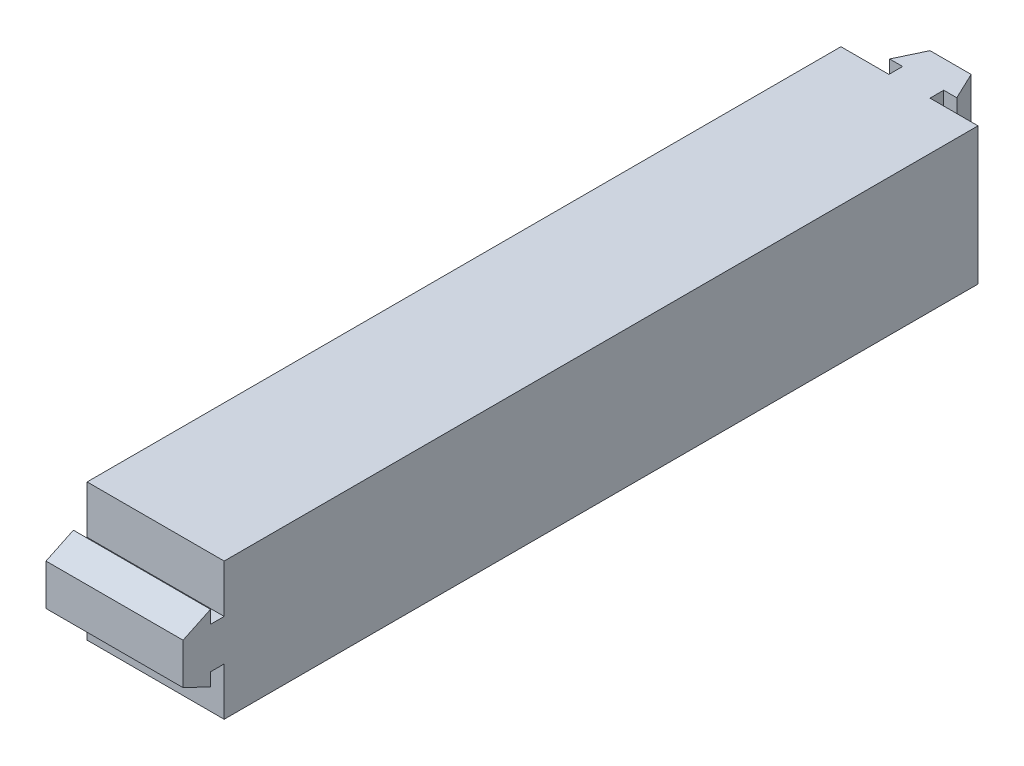
SolidWorks part; units mm, degrees
ref_plane "Front Plane" through (0, 0, 0) normal (0, 0, 1) x (1, 0, 0)
ref_plane "Top Plane" through (0, 0, 0) normal (0, 1, 0) x (1, 0, 0)
ref_plane "Right Plane" through (0, 0, 0) normal (1, 0, 0) x (0, 0, -1)
sketch "Sketch1" plane through (0, 0, 0) normal (0, 1, 0) x (1, 0, 0)
  line L1 (0, 0) -> (20, 0)
  line L2 (0, 0) -> (0, 110)
  line L4 (20, 0) -> (20, 110)
  line L5 (0, 110) -> (20, 110)
  point P1 (1.1497, 110)
  dimension "D1" = 110
  dimension "D4" = 20
extrude "Boss-Extrude1" add sketch "Sketch1" along normal blind 20
sketch "Sketch3" plane through (0, 0, 0) normal (1, 0, 0) x (0, 0, -1)
  line L0 (0, 10) -> (-6, 10) construction
  line L1 (0, 20) -> (0, 0) construction
  line L2 (0, 7) -> (0, 13)
  line L3 (0, 13) -> (-2, 13)
  line L4 (-2, 13) -> (-2, 14.9)
  line L5 (-2, 14.9) -> (-6, 13)
  line L6 (-6, 13) -> (-6, 7)
  line L7 (-2, 5.1) -> (-6, 7)
  line L8 (-2, 7) -> (-2, 5.1)
  line L9 (0, 7) -> (-2, 7)
  dimension "D1" = 6
  dimension "D2" = 3
  dimension "D3" = 2
  dimension "D4" = 1.9
  dimension "D5" = 3
extrude "Boss-Extrude3" add sketch "Sketch3" along normal up to surface (20 mm away) up to face at (20, 10, -55)
sketch "Sketch5" plane through (0, 20, 0) normal (0, 1, 0) x (1, 0, 0)
  line L0 (10, 110) -> (10, 116) construction
  line L1 (20, 110) -> (0, 110) construction
  line L2 (13, 110) -> (7, 110)
  line L3 (7, 110) -> (7, 112)
  line L4 (7, 112) -> (5.1, 112)
  line L5 (5.1, 112) -> (7, 116)
  line L6 (7, 116) -> (13, 116)
  line L7 (14.9, 112) -> (13, 116)
  line L8 (13, 112) -> (14.9, 112)
  line L9 (13, 110) -> (13, 112)
  dimension "D1" = 6
  dimension "D2" = 3
  dimension "D3" = 2
  dimension "D4" = 1.9
  dimension "D5" = 3
extrude "Boss-Extrude4" add sketch "Sketch5" against normal up to surface (20 mm away) up to face at (10, 0, -55)
